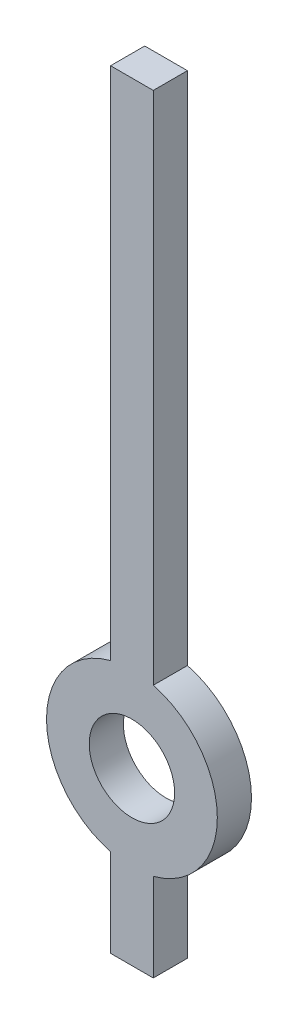
SolidWorks part; units mm, degrees
ref_plane "Front Plane" through (0, 0, 0) normal (0, 0, 1) x (1, 0, 0)
ref_plane "Top Plane" through (0, 0, 0) normal (0, 1, 0) x (1, 0, 0)
ref_plane "Right Plane" through (0, 0, 0) normal (1, 0, 0) x (0, 0, -1)
sketch "Croquis1" plane through (0, 0, 0) normal (0, 0, 1) x (1, 0, 0)
  line L0 (-0.125, -1) -> (-0.125, -0.4841)
  line L1 (-0.125, 3.5) -> (0.125, 3.5)
  line L2 (0.125, 3.5) -> (0.125, 0.4841)
  line L3 (0.125, -1) -> (-0.125, -1)
  line L4 (0.125, -0.4841) -> (0.125, -1)
  line L7 (-0.125, 0.4841) -> (-0.125, 3.5)
  arc A0 (0.125, -0.4841) -> (0.125, 0.4841) centre (0, 0) ccw
  circle A1 centre (0, 0) radius 0.25
  arc A2 (-0.125, 0.4841) -> (-0.125, -0.4841) centre (0, 0) ccw
  dimension "D1" = 1
  dimension "D2" = 0.5
  dimension "D4" = 0.25
  dimension "D5" = 1
  dimension "D6" = 4.5
extrude "Saliente-Extruir1" add sketch "Croquis1" along normal blind 0.2
